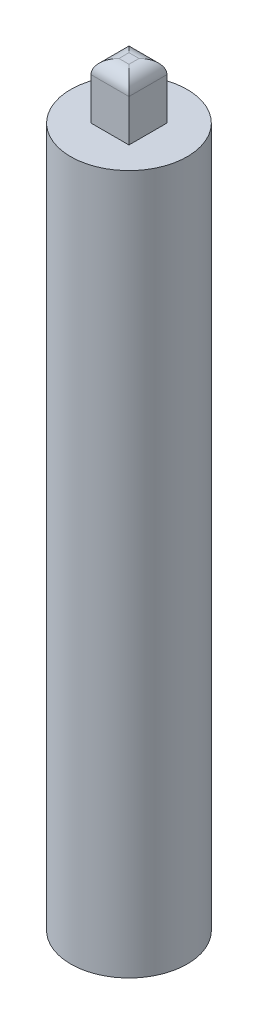
SolidWorks part; units mm, degrees
ref_plane "Front Plane" through (0, 0, 0) normal (0, 0, 1) x (1, 0, 0)
ref_plane "Top Plane" through (0, 0, 0) normal (0, 1, 0) x (1, 0, 0)
ref_plane "Right Plane" through (0, 0, 0) normal (1, 0, 0) x (0, 0, -1)
sketch "Sketch1" plane through (0, 0, 0) normal (0, 1, 0) x (1, 0, 0)
  circle A0 centre (0, 0) radius 12.5
  dimension "D1" = 25
extrude "Boss-Extrude1" add sketch "Sketch1" along normal blind 150
sketch "Sketch2" plane through (0, 150, 0) normal (0, 1, 0) x (1, 0, 0)
  line L1 (-4.075, 4.075) -> (4.075, 4.075)
  line L2 (-4.075, 4.075) -> (-4.075, -4.075)
  line L3 (-4.075, -4.075) -> (4.075, -4.075)
  line L4 (4.075, 4.075) -> (4.075, -4.075)
  line L5 (-4.075, 4.075) -> (4.075, -4.075) construction
  line L6 (-4.075, -4.075) -> (4.075, 4.075) construction
  point P0 (0, 0)
  dimension "D1" = 8.15
  dimension "D2" = 8.15
extrude "Boss-Extrude2" add sketch "Sketch2" along normal blind 12
fillet "Fillet1" radius 3 4 edges at (0, 162, -4.075) (4.075, 162, 0) (0, 162, 4.075) (-4.075, 162, 0)
sketch "Sketch3" plane through (0, 0, 0) normal (0, -1, 0) x (1, 0, 0)
  line L1 (4.1, -4.1) -> (-4.1, -4.1)
  line L2 (4.1, -4.1) -> (4.1, 4.1)
  line L3 (4.1, 4.1) -> (-4.1, 4.1)
  line L4 (-4.1, -4.1) -> (-4.1, 4.1)
  line L5 (4.1, -4.1) -> (-4.1, 4.1) construction
  line L6 (4.1, 4.1) -> (-4.1, -4.1) construction
  point P0 (0, 0)
  dimension "D1" = 8.2
  dimension "D2" = 8.2
extrude "Cut-Extrude1" cut sketch "Sketch3" against normal blind 20
